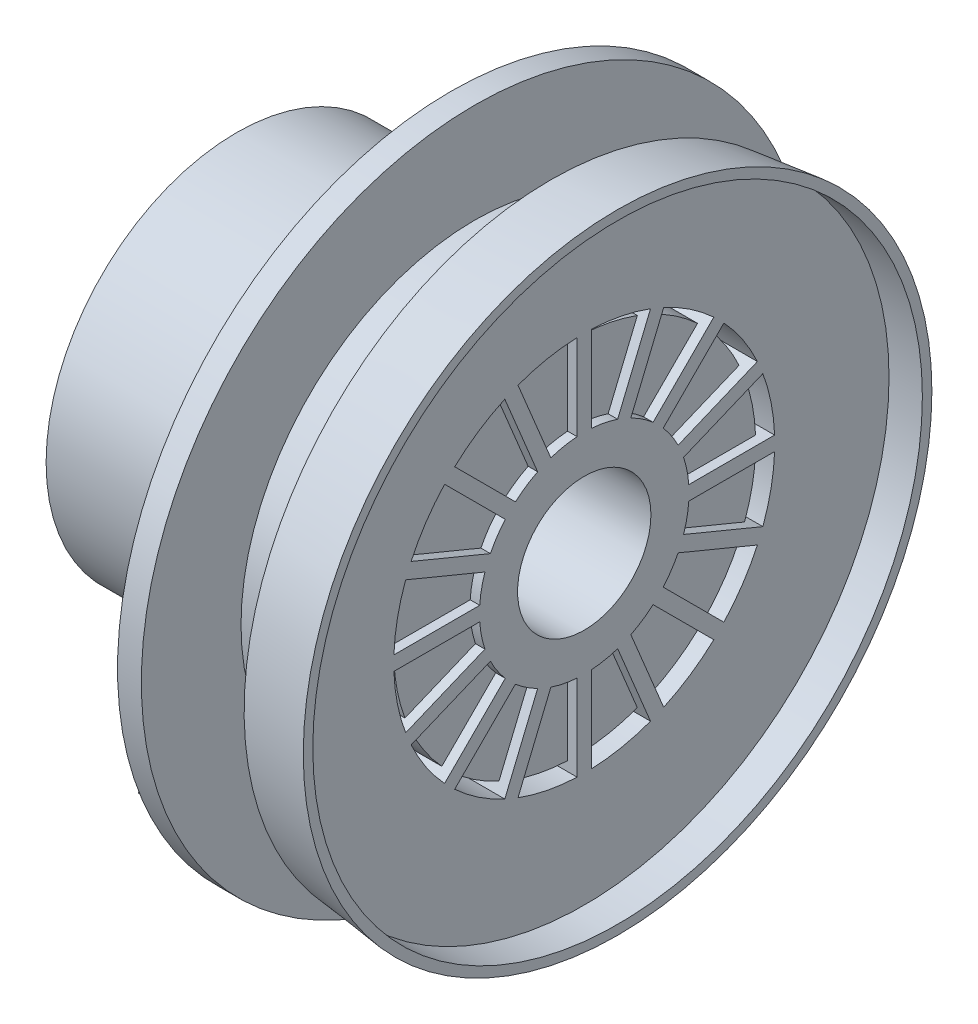
SolidWorks part; units mm, degrees
material "ABS PC"
ref_plane "Front Plane" through (0, 0, 0) normal (0, 0, 1) x (1, 0, 0)
ref_plane "Top Plane" through (0, 0, 0) normal (0, 1, 0) x (1, 0, 0)
ref_plane "Right Plane" through (0, 0, 0) normal (1, 0, 0) x (0, 0, -1)
sketch "Sketch2" plane through (0, 0, 0) normal (0, 0, 1) x (1, 0, 0)
  line L0 (0, 0) -> (-40, 0) construction
  line L1 (0, 0) -> (0, 33)
  line L2 (0, 0) -> (-40, 0)
  line L3 (-7, 32.2108) -> (-7, 24.5372)
  line L4 (-7, 24.5372) -> (-15, 24.5372)
  line L5 (-15, 24.5372) -> (-15, 35)
  line L6 (-15, 35) -> (-17.5, 35)
  line L7 (-17.5, 35) -> (-17.5, 20)
  line L8 (-17.5, 20) -> (-40, 20)
  line L9 (-40, 20) -> (-40, 0)
  line L10 (0, 33) -> (-7, 32.2108)
  dimension "D1" = 40
  dimension "D2" = 7
  dimension "D3" = 2.5
  dimension "D4" = 22.5
  dimension "D5" = 35
  dimension "D6" = 33
  dimension "D7" = 20
revolve "Revolve2" add sketch "Sketch2" angle 360 about L0
sketch "Sketch3" plane through (-17.5, 0, 0) normal (-1, 0, 0) x (0, 0, 1)
  line L0 (0, 0) -> (0, 35) construction
  line L3 (-1.1197, 19.9686) -> (-1.1197, 31.9523)
  line L4 (-1.1197, 31.9523) -> (1.3803, 31.9523)
  line L5 (1.3803, 19.9523) -> (1.3803, 31.9523)
  line L6 (-0.9476, 11.7944) -> (1.3803, 31.9523) construction
  line L7 (-1.1197, 31.9523) -> (0.773, 11.7488) construction
  circle A0 centre (0, 0) radius 35 construction
  circle A1 centre (0, 0) radius 20 construction
  arc A3 (1.3803, 19.9523) -> (-1.1197, 19.9686) centre (0, 0) ccw
  circle A4 centre (0, 0) radius 20 construction
  point P6 (0, 20)
  dimension "D1" = 2.5
  dimension "D2" = 12
extrude "Boss-Extrude1" add sketch "Sketch3" along normal blind 3
sketch "Sketch4" plane through (0, 0, 1.3803) normal (0, 0, 1) x (1, 0, 0)
  line L0 (-20.5, 19.9523) -> (-17.5, 31.9523)
  line L1 (-17.5, 31.9523) -> (-20.5, 31.9523)
  line L2 (-20.5, 31.9523) -> (-17.5, 31.9523) construction
  line L3 (-20.5, 31.9523) -> (-20.5, 19.9523)
extrude "Cut-Extrude1" cut sketch "Sketch4" against normal blind 10
pattern_circular "CirPattern1" count 6 over 360 about axis through (0, 0, 0) along (1, 0, 0) of "Boss-Extrude1", "Cut-Extrude1"
sketch "Sketch5" plane through (-17.5, 0, 0) normal (-1, 0, 0) x (0, 0, 1)
  line L0 (0, 0) -> (9.8867, -17.3854) construction
  line L1 (9.8867, -17.3854) -> (17.3017, -30.4245) construction
  line L2 (0.3414, -18.3449) -> (15.5915, -9.6726)
  line L3 (15.5915, -9.6726) -> (22.8287, -22.3988)
  line L4 (0.3414, -18.3449) -> (7.5786, -31.0712)
  line L5 (2.6596, -18.9823) -> (14.9541, -11.9907)
  line L6 (14.9541, -11.9907) -> (20.7029, -22.0997)
  line L7 (2.6596, -18.9823) -> (8.4083, -29.0913)
  arc A0 (1.1197, -19.9686) -> (16.5891, -11.1715) centre (0, 0) ccw construction
  circle A1 centre (0, 0) radius 35 construction
  arc A2 (7.5786, -31.0712) -> (22.8287, -22.3988) centre (0, 0) ccw
  arc A3 (8.4083, -29.0913) -> (20.7029, -22.0997) centre (0, 0) ccw
  point P12 (8.7073, -15.3114)
  dimension "D1" = 1.7
extrude "Boss-Extrude2" add sketch "Sketch5" along normal blind 10
sketch "Sketch6" plane through (0, 0, 0) normal (1, 0, 0) x (0, 0, -1)
  circle A0 centre (0, 0) radius 32
  dimension "D1" = 64
extrude "Cut-Extrude2" cut sketch "Sketch6" against normal blind 3.5
sketch "Sketch7" plane through (-3.5, 0, 0) normal (1, 0, 0) x (0, 0, -1)
  circle A0 centre (0, 0) radius 20
  circle A1 centre (0, 0) radius 11
  dimension "D1" = 40
  dimension "D2" = 22
extrude "Cut-Extrude4" cut sketch "Sketch7" against normal blind 5.5
sketch "Sketch9" plane through (-9, 0, 0) normal (1, 0, 0) x (0, 0, -1)
  line L0 (0.75, 10.6043) -> (0.75, 20.3654)
  line L5 (-0.75, -21.4633) -> (0.75, 21.4633) construction
  line L6 (-0.75, 21.4633) -> (0.75, -21.4633) construction
  line L7 (-0.75, 10.6043) -> (-0.75, 20.3654)
  arc A0 (0.75, 10.6043) -> (-0.75, 10.6043) centre (0, 0) ccw
  arc A3 (0.75, 20.3654) -> (-0.75, 20.3654) centre (0, 0) ccw
  point P0 (0, 0)
  dimension "D1" = 1.5
extrude "Boss-Extrude3" add sketch "Sketch9" along normal blind 5.5
pattern_circular "CirPattern2" count 16 over 360 about axis through (0, 0, 0) along (1, 0, 0) of "Boss-Extrude3"
sketch "Sketch10" plane through (-9, 0, 0) normal (1, 0, 0) x (0, 0, -1)
  circle A0 centre (0, 0) radius 19
  dimension "D1" = 38
extrude "Boss-Extrude4" add sketch "Sketch10" along normal blind 4.5
sketch "Sketch11" plane through (-40, 0, 0) normal (-1, 0, 0) x (0, 0, 1)
  circle A0 centre (0, 0) radius 18
  dimension "D1" = 36
extrude "Cut-Extrude5" cut sketch "Sketch11" against normal blind 25.5
sketch "Sketch12" plane through (-14.5, 0, 0) normal (-1, 0, 0) x (0, 0, 1)
  circle A0 centre (0, 0) radius 7
  circle A1 centre (0, 0) radius 8
  dimension "D1" = 14
  dimension "D2" = 16
extrude "Boss-Extrude5" add sketch "Sketch12" along normal blind 5
sketch "Sketch13" plane through (-14.5, 0, 0) normal (-1, 0, 0) x (0, 0, 1)
  circle A0 centre (0, 0) radius 7
extrude "Cut-Extrude6" cut sketch "Sketch13" against normal blind 23
sketch "Sketch14" plane through (-15, 0, 0) normal (1, 0, 0) x (0, 0, -1)
  line L0 (-14.9695, -26.3234) -> (-12.1296, -21.3295) construction
  circle A0 centre (0, 0) radius 35 construction
  circle A3 centre (0, 0) radius 24.5372 construction
  arc A4 (-20.7029, -22.0997) -> (-8.4083, -29.0913) centre (0, 0) ccw construction
  circle A5 centre (-13.5496, -23.8264) radius 2
extrude "Cut-Extrude9" cut sketch "Sketch14" against normal blind 6
